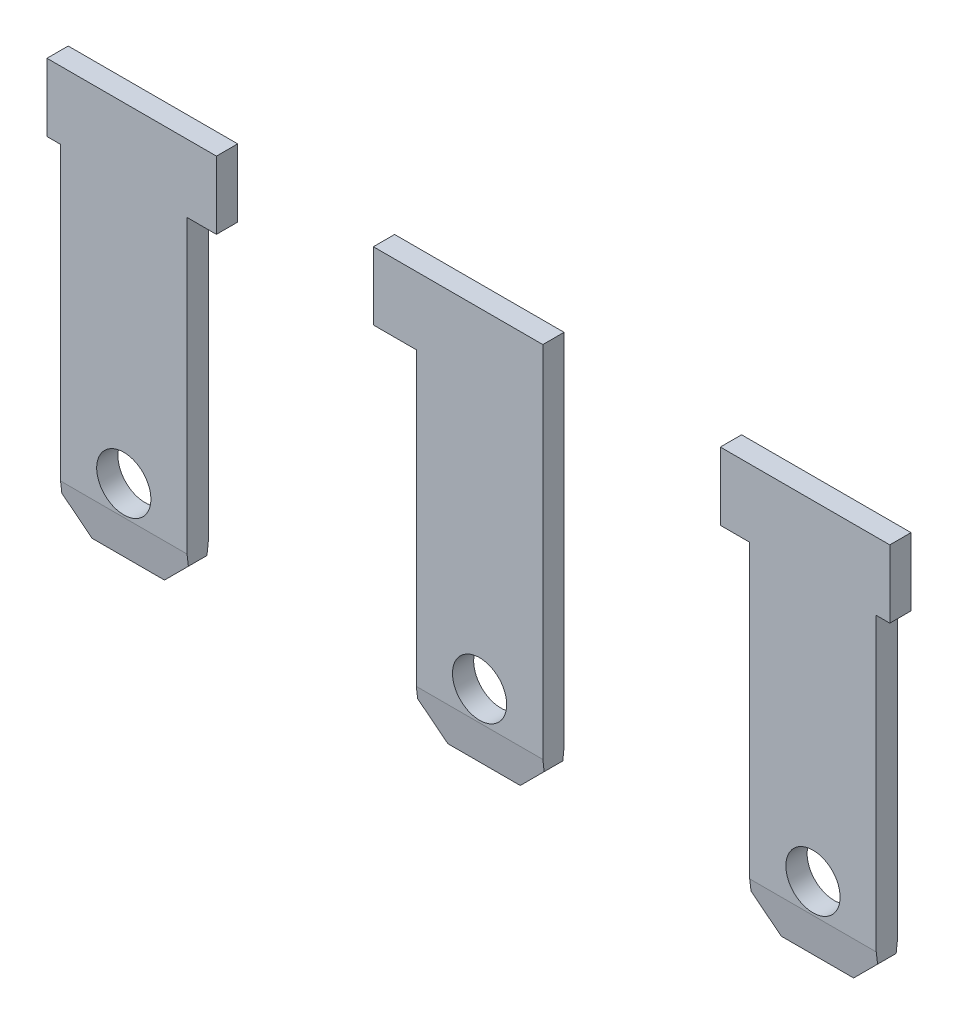
SolidWorks part; units mm, degrees
ref_plane "Front Plane" through (0, 0, 0) normal (0, 0, 1) x (1, 0, 0)
ref_plane "Top Plane" through (0, 0, 0) normal (0, 1, 0) x (1, 0, 0)
ref_plane "Right Plane" through (0, 0, 0) normal (1, 0, 0) x (0, 0, -1)
sketch "Sketch1" plane through (0, 0, 0) normal (0, 0, 1) x (1, 0, 0)
  line L6 (-9.4849, -12.3806) -> (16.1475, -12.3806) construction
  line L7 (-7.4571, -3.5806) -> (-3.7071, -3.5806)
  line L8 (-7.4571, -3.5806) -> (-7.4571, -5.0806)
  line L9 (-7.4571, -5.0806) -> (-7.1571, -5.0806)
  line L10 (-3.7071, -3.5806) -> (-3.7071, -5.0806)
  line L11 (-0.2345, -3.5806) -> (3.5155, -3.5806)
  line L12 (-0.2345, -3.5806) -> (-0.2345, -5.0806)
  line L13 (-0.2345, -5.0806) -> (0.7155, -5.0806)
  line L14 (3.5155, -3.5806) -> (3.5155, -5.0806)
  line L15 (11.1929, -3.5806) -> (7.4429, -3.5806)
  line L16 (11.1929, -3.5806) -> (11.1929, -5.0806)
  line L17 (11.1929, -5.0806) -> (10.8929, -5.0806)
  line L18 (7.4429, -3.5806) -> (7.4429, -5.0806)
  line L27 (-4.3571, -5.0806) -> (-3.7071, -5.0806)
  line L29 (10.8929, -5.0806) -> (10.8929, -11.7806)
  line L30 (10.2929, -12.3806) -> (8.6929, -12.3806)
  line L31 (8.0929, -5.0806) -> (8.0929, -11.7806)
  line L33 (3.5155, -5.0806) -> (3.5155, -11.7806)
  line L34 (2.9155, -12.3806) -> (1.3155, -12.3806)
  line L35 (0.7155, -5.0806) -> (0.7155, -11.7806)
  line L37 (-7.1571, -5.0806) -> (-7.1571, -11.7806)
  line L38 (-6.5571, -12.3806) -> (-4.9571, -12.3806)
  line L39 (-4.3571, -5.0806) -> (-4.3571, -11.7806)
  line L44 (8.0929, -5.0806) -> (7.4429, -5.0806)
  line L45 (-7.1571, -11.7806) -> (-6.5571, -12.3806)
  line L46 (-4.9571, -12.3806) -> (-4.3571, -11.7806)
  line L47 (1.3155, -12.3806) -> (0.7155, -11.7806)
  line L48 (3.5155, -11.7806) -> (2.9155, -12.3806)
  line L49 (8.6929, -12.3806) -> (8.0929, -11.7806)
  line L50 (10.8929, -11.7806) -> (10.2929, -12.3806)
  circle A0 centre (-5.7571, -10.8806) radius 0.6
  circle A1 centre (2.1155, -10.8806) radius 0.6
  circle A2 centre (9.4929, -10.8806) radius 0.6
  point P29 (8.0929, -12.3806)
  point P30 (10.8929, -12.3806)
  point P32 (0.7155, -12.3806)
  point P33 (3.5155, -12.3806)
  point P36 (-4.3571, -12.3806)
  point P37 (-7.1571, -12.3806)
  point P46 (1.7847, -3.5806)
  dimension "D3" = 1.3155
  dimension "D4" = 1.7847
  dimension "D5" = 2.1155
  dimension "D1" = 1.2
  dimension "D2" = 0.7155
  dimension "D6" = 2.9155
  dimension "D7" = 7.4429
  dimension "D8" = 8.0929
  dimension "D9" = 11.1929
  dimension "D10" = 3.7071
  dimension "D11" = 9.4929
  dimension "D12" = 3.5806
  dimension "D13" = 5.0806
  dimension "D14" = 10.8806
  dimension "D15" = 11.7806
  dimension "D19" = 5.7571
extrude "Boss-Extrude1" add sketch "Sketch1" along normal blind 0.47
sketch "Sketch2" plane through (0, 0, 0) normal (1, 0, 0) x (0, 0, -1)
  line L0 (-2.8437, -11.5306) -> (3.9368, -11.5306) construction
  line L1 (-0.47, -12.3806) -> (0, -12.3806) construction
  line L2 (-0.47, -11.5306) -> (-0.37, -12.3806)
  line L3 (-0.47, -11.7806) -> (-0.47, -5.0806) construction
  line L4 (-0.37, -12.3806) -> (-0.47, -12.3806)
  line L5 (-0.47, -12.3806) -> (-0.47, -11.5306)
  line L6 (-0.235, -12.8717) -> (-0.235, -0.7291) construction
  line L7 (-0.1, -12.3806) -> (0, -12.3806)
  line L8 (0, -11.5306) -> (-0.1, -12.3806)
  line L9 (0, -12.3806) -> (0, -11.5306)
  dimension "D1" = 0.85
  dimension "D2" = 0.1
extrude "Cut-Extrude1" cut sketch "Sketch2" against normal through all both and the other way through all
ref_plane "Plane1" through (0, 0, 0.235) normal (0, 0, 1) x (1, 0, 0)
